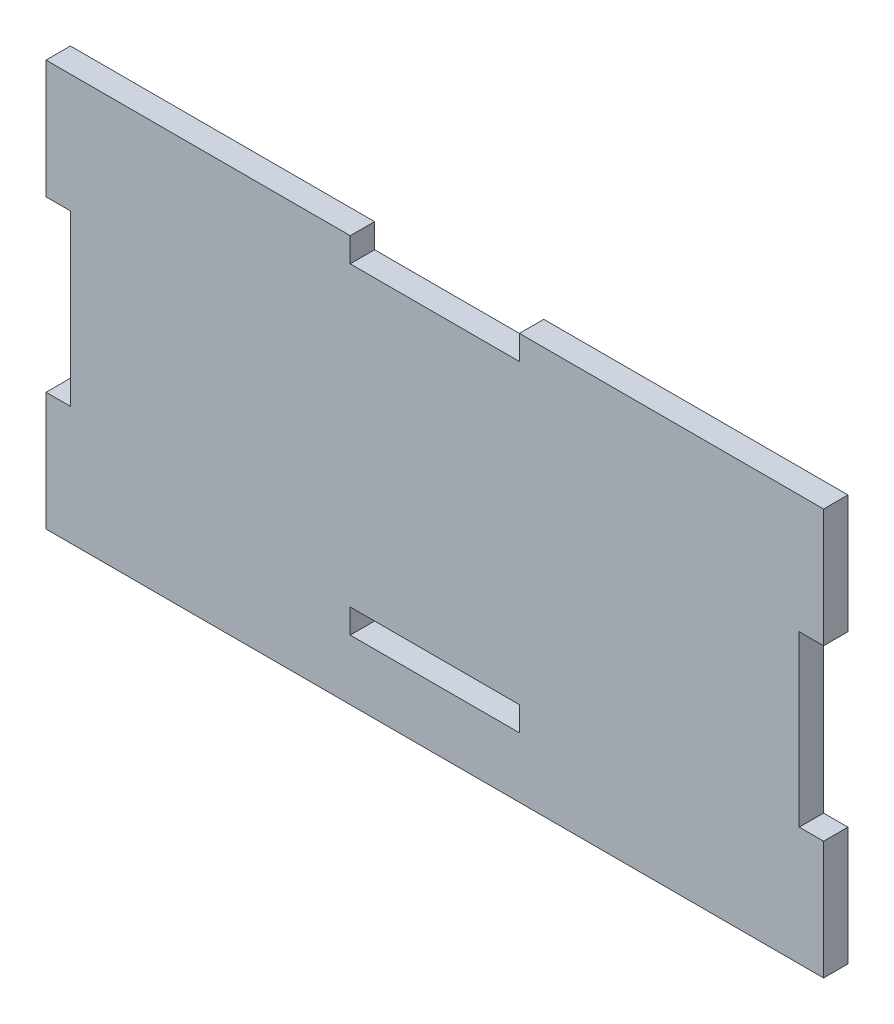
SolidWorks part; units mm, degrees
ref_plane "Front Plane" through (0, 0, 0) normal (0, 0, 1) x (1, 0, 0)
ref_plane "Top Plane" through (0, 0, 0) normal (0, 1, 0) x (1, 0, 0)
ref_plane "Right Plane" through (0, 0, 0) normal (1, 0, 0) x (0, 0, -1)
sketch "Sketch1" plane through (0, 0, 0) normal (0, 0, 1) x (1, 0, 0)
  line L0 (0, -14.7066) -> (0, 0) construction
  line L1 (43.7642, -22.86) -> (-43.7642, -22.86)
  line L2 (43.7642, -22.86) -> (43.7642, 22.86)
  line L3 (43.7642, 22.86) -> (-43.7642, 22.86)
  line L4 (-43.7642, -22.86) -> (-43.7642, 22.86)
  line L5 (43.7642, -22.86) -> (-43.7642, 22.86) construction
  line L6 (43.7642, 22.86) -> (-43.7642, -22.86) construction
  line L7 (-9.525, -16.0782) -> (9.525, -16.0782)
  line L8 (-9.525, -16.0782) -> (-9.525, -13.335)
  line L9 (-9.525, -13.335) -> (9.525, -13.335)
  line L10 (9.525, -16.0782) -> (9.525, -13.335)
  line L11 (-9.525, -16.0782) -> (9.525, -13.335) construction
  line L12 (-9.525, -13.335) -> (9.525, -16.0782) construction
  point P1 (0, 0)
  point P6 (0, -14.7066)
  dimension "D1" = 87.5284
  dimension "D2" = 45.72
  dimension "D3" = 19.05
  dimension "D4" = 2.7432
  dimension "D5" = 9.525
extrude "Boss-Extrude1" add sketch "Sketch1" along normal blind 2.7432
sketch "Sketch2" plane through (0, 0, 2.7432) normal (0, 0, 1) x (1, 0, 0)
  line L0 (-43.7642, 0) -> (43.7642, 0) construction
  line L1 (-43.7642, 22.86) -> (-43.7642, -22.86) construction
  line L2 (43.7642, -22.86) -> (43.7642, 22.86) construction
  line L3 (0, 0) -> (0, 22.86) construction
  line L4 (-41.021, -9.525) -> (-43.7642, -9.525)
  line L5 (-41.021, -9.525) -> (-41.021, 9.525)
  line L6 (-41.021, 9.525) -> (-43.7642, 9.525)
  line L7 (-43.7642, -9.525) -> (-43.7642, 9.525)
  line L8 (-41.021, -9.525) -> (-43.7642, 9.525) construction
  line L9 (-41.021, 9.525) -> (-43.7642, -9.525) construction
  line L10 (41.021, 9.525) -> (43.7642, 9.525)
  line L11 (41.021, 9.525) -> (41.021, -9.525)
  line L12 (41.021, -9.525) -> (43.7642, -9.525)
  line L13 (43.7642, 9.525) -> (43.7642, -9.525)
  line L14 (41.021, 9.525) -> (43.7642, -9.525) construction
  line L15 (41.021, -9.525) -> (43.7642, 9.525) construction
  line L16 (43.7642, 22.86) -> (-43.7642, 22.86) construction
  line L18 (9.525, 20.1168) -> (-9.525, 20.1168)
  line L19 (9.525, 20.1168) -> (9.525, 22.86)
  line L20 (9.525, 22.86) -> (-9.525, 22.86)
  line L21 (-9.525, 20.1168) -> (-9.525, 22.86)
  line L22 (9.525, 20.1168) -> (-9.525, 22.86) construction
  line L23 (9.525, 22.86) -> (-9.525, 20.1168) construction
  point P6 (-42.3926, 0)
  point P11 (42.3926, 0)
  point P20 (0, 21.4884)
  dimension "D1" = 19.05
  dimension "D2" = 2.7432
extrude "Cut-Extrude1" cut sketch "Sketch2" against normal through all
